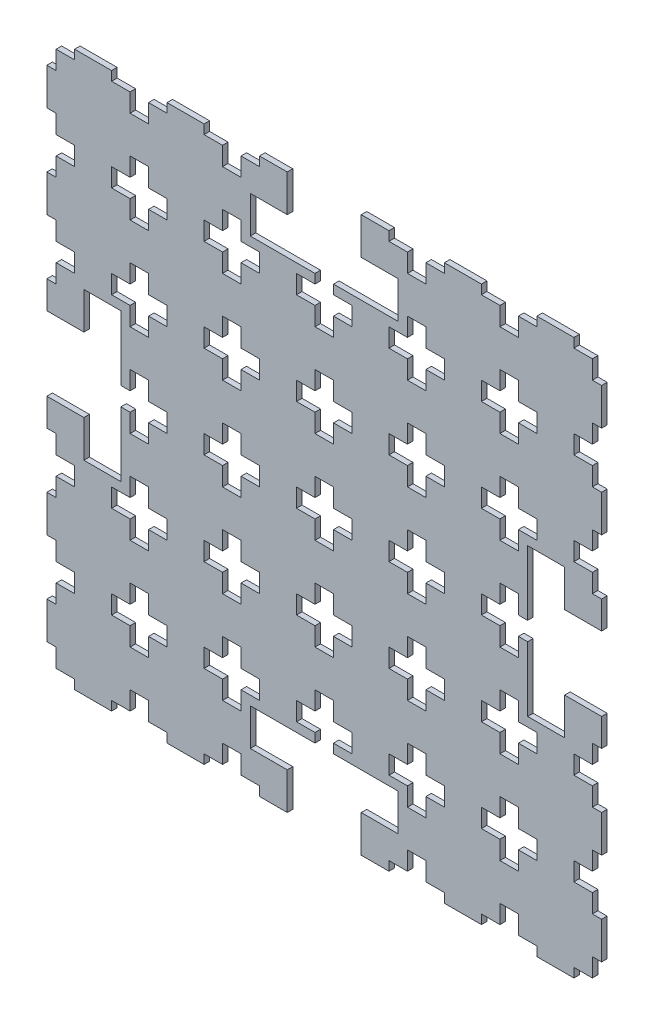
SolidWorks part; units mm, degrees
ref_plane "Plan de face" through (0, 0, 0) normal (0, 0, 1) x (1, 0, 0)
ref_plane "Plan de dessus" through (0, 0, 0) normal (0, 1, 0) x (1, 0, 0)
ref_plane "Plan de droite" through (0, 0, 0) normal (1, 0, 0) x (0, 0, -1)
sketch "Esquisse1" plane through (0, 0, 0) normal (0, 0, 1) x (1, 0, 0)
  line L1 (-218.6403, 173.0618) -> (81.3597, 173.0618)
  line L2 (-218.6403, 173.0618) -> (-218.6403, -126.9382)
  line L3 (-218.6403, -126.9382) -> (81.3597, -126.9382)
  line L4 (81.3597, 173.0618) -> (81.3597, -126.9382)
  dimension "D1" = 300
  dimension "D2" = 300
extrude "Boss.-Extru.1" add sketch "Esquisse1" along normal blind 3
sketch "Esquisse2" plane through (0, 0, 0) normal (0, 0, -1) x (-1, 0, 0)
  line L0 (-81.3597, 138.0618) -> (-76.3597, 138.0618)
  line L1 (183.6403, 173.0618) -> (183.6403, 168.0618)
  line L2 (-81.3597, -126.9382) -> (-81.3597, 173.0618) construction
  line L3 (-76.3597, 138.0618) -> (-76.3597, 128.0618)
  line L4 (-76.3597, 128.0618) -> (-66.3597, 128.0618)
  line L5 (-66.3597, 128.0618) -> (-66.3597, 118.0618)
  line L6 (-66.3597, 118.0618) -> (-76.3597, 118.0618)
  line L7 (-76.3597, 118.0618) -> (-76.3597, 108.0618)
  line L8 (13.6403, 128.0618) -> (13.6403, 138.0618)
  line L9 (-76.3597, 108.0618) -> (-81.3597, 108.0618)
  line L10 (-81.3597, 88.0618) -> (-76.3597, 88.0618)
  line L11 (-76.3597, 88.0618) -> (-76.3597, 78.0618)
  line L12 (-76.3597, 78.0618) -> (-66.3597, 78.0618)
  line L13 (-66.3597, 78.0618) -> (-66.3597, 68.0618)
  line L14 (-66.3597, 68.0618) -> (-76.3597, 68.0618)
  line L15 (-76.3597, 68.0618) -> (-76.3597, 58.0618)
  line L16 (-76.3597, 58.0618) -> (-81.3597, 58.0618)
  line L17 (-81.3597, 38.0618) -> (-76.3597, 38.0618)
  line L18 (-76.3597, 38.0618) -> (-76.3597, 28.0618)
  line L19 (-76.3597, 28.0618) -> (-66.3597, 28.0618)
  line L20 (-66.3597, 28.0618) -> (-66.3597, 18.0618)
  line L21 (-66.3597, 18.0618) -> (-76.3597, 18.0618)
  line L22 (-76.3597, 18.0618) -> (-76.3597, 8.0618)
  line L23 (-76.3597, 8.0618) -> (-81.3597, 8.0618)
  line L24 (-81.3597, -11.9382) -> (-76.3597, -11.9382)
  line L25 (-76.3597, -11.9382) -> (-76.3597, -21.9382)
  line L26 (-76.3597, -21.9382) -> (-66.3597, -21.9382)
  line L27 (-66.3597, -21.9382) -> (-66.3597, -31.9382)
  line L28 (-66.3597, -31.9382) -> (-76.3597, -31.9382)
  line L29 (-76.3597, -31.9382) -> (-76.3597, -41.9382)
  line L30 (-76.3597, -41.9382) -> (-81.3597, -41.9382)
  line L31 (-81.3597, -61.9382) -> (-76.3597, -61.9382)
  line L32 (-76.3597, -61.9382) -> (-76.3597, -71.9382)
  line L33 (-76.3597, -71.9382) -> (-66.3597, -71.9382)
  line L34 (-66.3597, -71.9382) -> (-66.3597, -81.9382)
  line L35 (-66.3597, -81.9382) -> (-76.3597, -81.9382)
  line L36 (-76.3597, -81.9382) -> (-76.3597, -91.9382)
  line L37 (-76.3597, -91.9382) -> (-81.3597, -91.9382)
  line L38 (-81.3597, -111.9382) -> (-76.3597, -111.9382)
  line L39 (-76.3597, -111.9382) -> (-76.3597, -121.9382)
  line L40 (-76.3597, -121.9382) -> (-66.3597, -121.9382)
  line L41 (-66.3597, -121.9382) -> (-66.3597, -126.9382)
  line L42 (218.6403, -126.9382) -> (-81.3597, -126.9382) construction
  line L43 (-81.3597, 173.0618) -> (218.6403, 173.0618) construction
  line L44 (-81.3597, 173.0618) -> (218.6403, 173.0618) construction
  line L45 (-66.3597, -131.9382) -> (-76.3597, -131.9382) [skipped]
  line L46 (-76.3597, -131.9382) -> (-76.3597, -141.9382) [skipped]
  line L47 (-76.3597, -141.9382) -> (-81.3597, -141.9382) [skipped]
  line L48 (-66.3597, -121.9382) -> (-66.3597, -131.9382) [skipped]
  line L49 (183.6403, 168.0618) -> (173.6403, 168.0618)
  line L50 (173.6403, 168.0618) -> (173.6403, 158.0618)
  line L51 (173.6403, 158.0618) -> (163.6403, 158.0618)
  line L52 (163.6403, 158.0618) -> (163.6403, 168.0618)
  line L53 (163.6403, 168.0618) -> (153.6403, 168.0618)
  line L54 (153.6403, 168.0618) -> (153.6403, 173.0618)
  line L55 (153.6403, 173.0618) -> (183.6403, 173.0618)
  line L56 (133.6403, 173.0618) -> (133.6403, 168.0618)
  line L57 (133.6403, 168.0618) -> (123.6403, 168.0618)
  line L58 (123.6403, 168.0618) -> (123.6403, 158.0618)
  line L59 (123.6403, 158.0618) -> (113.6403, 158.0618)
  line L60 (113.6403, 158.0618) -> (113.6403, 168.0618)
  line L61 (-36.3597, 128.0618) -> (-36.3597, 138.0618)
  line L62 (-36.3597, 138.0618) -> (-26.3597, 138.0618)
  line L63 (-26.3597, 138.0618) -> (-26.3597, 128.0618)
  line L64 (-26.3597, 128.0618) -> (-16.3597, 128.0618)
  line L65 (-16.3597, 128.0618) -> (-16.3597, 118.0618)
  line L66 (13.6403, 138.0618) -> (23.6403, 138.0618)
  line L67 (3.6403, 128.0618) -> (13.6403, 128.0618)
  line L68 (3.6403, 118.0618) -> (3.6403, 128.0618)
  line L69 (13.6403, 118.0618) -> (3.6403, 118.0618)
  line L70 (13.6403, 108.0618) -> (13.6403, 118.0618)
  line L71 (23.6403, 108.0618) -> (13.6403, 108.0618)
  line L72 (23.6403, 118.0618) -> (23.6403, 108.0618)
  line L73 (33.6403, 118.0618) -> (23.6403, 118.0618)
  line L74 (33.6403, 128.0618) -> (33.6403, 118.0618)
  line L75 (23.6403, 128.0618) -> (33.6403, 128.0618)
  line L76 (23.6403, 138.0618) -> (23.6403, 128.0618)
  line L77 (63.6403, 128.0618) -> (63.6403, 138.0618)
  line L78 (63.6403, 138.0618) -> (73.6403, 138.0618)
  line L79 (53.6403, 128.0618) -> (63.6403, 128.0618)
  line L80 (53.6403, 118.0618) -> (53.6403, 128.0618)
  line L81 (63.6403, 118.0618) -> (53.6403, 118.0618)
  line L82 (63.6403, 108.0618) -> (63.6403, 118.0618)
  line L83 (73.6403, 108.0618) -> (63.6403, 108.0618)
  line L84 (73.6403, 118.0618) -> (73.6403, 108.0618)
  line L85 (83.6403, 118.0618) -> (73.6403, 118.0618)
  line L86 (83.6403, 128.0618) -> (83.6403, 118.0618)
  line L87 (73.6403, 128.0618) -> (83.6403, 128.0618)
  line L88 (73.6403, 138.0618) -> (73.6403, 128.0618)
  line L89 (113.6403, 128.0618) -> (113.6403, 138.0618)
  line L90 (113.6403, 138.0618) -> (123.6403, 138.0618)
  line L91 (103.6403, 128.0618) -> (113.6403, 128.0618)
  line L92 (103.6403, 118.0618) -> (103.6403, 128.0618)
  line L93 (113.6403, 118.0618) -> (103.6403, 118.0618)
  line L94 (113.6403, 108.0618) -> (113.6403, 118.0618)
  line L95 (123.6403, 108.0618) -> (113.6403, 108.0618)
  line L96 (123.6403, 118.0618) -> (123.6403, 108.0618)
  line L97 (133.6403, 118.0618) -> (123.6403, 118.0618)
  line L98 (133.6403, 128.0618) -> (133.6403, 118.0618)
  line L99 (123.6403, 128.0618) -> (133.6403, 128.0618)
  line L100 (123.6403, 138.0618) -> (123.6403, 128.0618)
  line L101 (163.6403, 128.0618) -> (163.6403, 138.0618)
  line L102 (163.6403, 138.0618) -> (173.6403, 138.0618)
  line L103 (153.6403, 128.0618) -> (163.6403, 128.0618)
  line L104 (153.6403, 118.0618) -> (153.6403, 128.0618)
  line L105 (163.6403, 118.0618) -> (153.6403, 118.0618)
  line L106 (163.6403, 108.0618) -> (163.6403, 118.0618)
  line L107 (173.6403, 108.0618) -> (163.6403, 108.0618)
  line L108 (173.6403, 118.0618) -> (173.6403, 108.0618)
  line L109 (183.6403, 118.0618) -> (173.6403, 118.0618)
  line L110 (183.6403, 128.0618) -> (183.6403, 118.0618)
  line L111 (173.6403, 128.0618) -> (183.6403, 128.0618)
  line L112 (173.6403, 138.0618) -> (173.6403, 128.0618)
  line L113 (213.6403, 128.0618) -> (213.6403, 138.0618)
  line L114 (213.6403, 138.0618) -> (223.6403, 138.0618)
  line L115 (203.6403, 128.0618) -> (213.6403, 128.0618)
  line L116 (203.6403, 118.0618) -> (203.6403, 128.0618)
  line L117 (213.6403, 118.0618) -> (203.6403, 118.0618)
  line L118 (213.6403, 108.0618) -> (213.6403, 118.0618)
  line L119 (223.6403, 108.0618) -> (213.6403, 108.0618)
  line L120 (223.6403, 118.0618) -> (223.6403, 108.0618)
  line L121 (233.6403, 118.0618) -> (223.6403, 118.0618)
  line L122 (233.6403, 128.0618) -> (233.6403, 118.0618)
  line L123 (223.6403, 128.0618) -> (233.6403, 128.0618)
  line L124 (223.6403, 138.0618) -> (223.6403, 128.0618)
  line L125 (113.6403, 168.0618) -> (103.6403, 168.0618)
  line L126 (103.6403, 168.0618) -> (103.6403, 173.0618)
  line L127 (103.6403, 173.0618) -> (133.6403, 173.0618)
  line L128 (83.6403, 173.0618) -> (83.6403, 168.0618)
  line L129 (83.6403, 168.0618) -> (73.6403, 168.0618)
  line L130 (73.6403, 168.0618) -> (73.6403, 158.0618)
  line L131 (73.6403, 158.0618) -> (63.6403, 158.0618)
  line L132 (63.6403, 158.0618) -> (63.6403, 168.0618)
  line L133 (63.6403, 168.0618) -> (53.6403, 168.0618)
  line L134 (53.6403, 168.0618) -> (53.6403, 173.0618)
  line L135 (83.6403, 173.0618) -> (53.6403, 173.0618)
  line L136 (33.6403, 173.0618) -> (33.6403, 168.0618)
  line L137 (33.6403, 168.0618) -> (23.6403, 168.0618)
  line L138 (23.6403, 168.0618) -> (23.6403, 158.0618)
  line L139 (23.6403, 158.0618) -> (13.6403, 158.0618)
  line L140 (13.6403, 158.0618) -> (13.6403, 168.0618)
  line L141 (13.6403, 168.0618) -> (3.6403, 168.0618)
  line L142 (3.6403, 168.0618) -> (3.6403, 173.0618)
  line L143 (33.6403, 173.0618) -> (3.6403, 173.0618)
  line L144 (-16.3597, 173.0618) -> (-16.3597, 168.0618)
  line L145 (-16.3597, 168.0618) -> (-26.3597, 168.0618)
  line L146 (-26.3597, 168.0618) -> (-26.3597, 158.0618)
  line L147 (-26.3597, 158.0618) -> (-36.3597, 158.0618)
  line L148 (-36.3597, 158.0618) -> (-36.3597, 168.0618)
  line L149 (-36.3597, 168.0618) -> (-46.3597, 168.0618)
  line L150 (-46.3597, 168.0618) -> (-46.3597, 173.0618)
  line L151 (-46.3597, 173.0618) -> (-16.3597, 173.0618)
  line L180 (218.6403, 173.0618) -> (218.6403, -126.9382) construction
  line L186 (13.6403, 78.0618) -> (13.6403, 88.0618)
  line L187 (13.6403, 88.0618) -> (23.6403, 88.0618)
  line L188 (3.6403, 78.0618) -> (13.6403, 78.0618)
  line L189 (3.6403, 68.0618) -> (3.6403, 78.0618)
  line L190 (13.6403, 68.0618) -> (3.6403, 68.0618)
  line L191 (13.6403, 58.0618) -> (13.6403, 68.0618)
  line L192 (23.6403, 58.0618) -> (13.6403, 58.0618)
  line L193 (23.6403, 68.0618) -> (23.6403, 58.0618)
  line L194 (33.6403, 68.0618) -> (23.6403, 68.0618)
  line L195 (33.6403, 78.0618) -> (33.6403, 68.0618)
  line L196 (23.6403, 78.0618) -> (33.6403, 78.0618)
  line L197 (23.6403, 88.0618) -> (23.6403, 78.0618)
  line L198 (63.6403, 78.0618) -> (63.6403, 88.0618)
  line L199 (63.6403, 88.0618) -> (73.6403, 88.0618)
  line L200 (53.6403, 78.0618) -> (63.6403, 78.0618)
  line L201 (53.6403, 68.0618) -> (53.6403, 78.0618)
  line L202 (63.6403, 68.0618) -> (53.6403, 68.0618)
  line L203 (63.6403, 58.0618) -> (63.6403, 68.0618)
  line L204 (73.6403, 58.0618) -> (63.6403, 58.0618)
  line L205 (73.6403, 68.0618) -> (73.6403, 58.0618)
  line L206 (83.6403, 68.0618) -> (73.6403, 68.0618)
  line L207 (83.6403, 78.0618) -> (83.6403, 68.0618)
  line L208 (73.6403, 78.0618) -> (83.6403, 78.0618)
  line L209 (73.6403, 88.0618) -> (73.6403, 78.0618)
  line L210 (113.6403, 78.0618) -> (113.6403, 88.0618)
  line L211 (113.6403, 88.0618) -> (123.6403, 88.0618)
  line L212 (103.6403, 78.0618) -> (113.6403, 78.0618)
  line L213 (103.6403, 68.0618) -> (103.6403, 78.0618)
  line L214 (113.6403, 68.0618) -> (103.6403, 68.0618)
  line L215 (113.6403, 58.0618) -> (113.6403, 68.0618)
  line L216 (123.6403, 58.0618) -> (113.6403, 58.0618)
  line L217 (123.6403, 68.0618) -> (123.6403, 58.0618)
  line L218 (133.6403, 68.0618) -> (123.6403, 68.0618)
  line L219 (133.6403, 78.0618) -> (133.6403, 68.0618)
  line L220 (123.6403, 78.0618) -> (133.6403, 78.0618)
  line L221 (123.6403, 88.0618) -> (123.6403, 78.0618)
  line L222 (163.6403, 78.0618) -> (163.6403, 88.0618)
  line L223 (163.6403, 88.0618) -> (173.6403, 88.0618)
  line L224 (153.6403, 78.0618) -> (163.6403, 78.0618)
  line L225 (153.6403, 68.0618) -> (153.6403, 78.0618)
  line L226 (163.6403, 68.0618) -> (153.6403, 68.0618)
  line L227 (163.6403, 58.0618) -> (163.6403, 68.0618)
  line L228 (173.6403, 58.0618) -> (163.6403, 58.0618)
  line L229 (173.6403, 68.0618) -> (173.6403, 58.0618)
  line L230 (183.6403, 68.0618) -> (173.6403, 68.0618)
  line L231 (183.6403, 78.0618) -> (183.6403, 68.0618)
  line L232 (173.6403, 78.0618) -> (183.6403, 78.0618)
  line L233 (173.6403, 88.0618) -> (173.6403, 78.0618)
  line L234 (213.6403, 78.0618) -> (213.6403, 88.0618)
  line L235 (213.6403, 88.0618) -> (223.6403, 88.0618)
  line L236 (203.6403, 78.0618) -> (213.6403, 78.0618)
  line L237 (203.6403, 68.0618) -> (203.6403, 78.0618)
  line L238 (213.6403, 68.0618) -> (203.6403, 68.0618)
  line L239 (213.6403, 58.0618) -> (213.6403, 68.0618)
  line L240 (223.6403, 58.0618) -> (213.6403, 58.0618)
  line L241 (223.6403, 68.0618) -> (223.6403, 58.0618)
  line L242 (233.6403, 68.0618) -> (223.6403, 68.0618)
  line L243 (233.6403, 78.0618) -> (233.6403, 68.0618)
  line L244 (223.6403, 78.0618) -> (233.6403, 78.0618)
  line L245 (223.6403, 88.0618) -> (223.6403, 78.0618)
  line L246 (13.6403, 28.0618) -> (13.6403, 38.0618)
  line L247 (13.6403, 38.0618) -> (23.6403, 38.0618)
  line L248 (3.6403, 28.0618) -> (13.6403, 28.0618)
  line L249 (3.6403, 18.0618) -> (3.6403, 28.0618)
  line L250 (13.6403, 18.0618) -> (3.6403, 18.0618)
  line L251 (13.6403, 8.0618) -> (13.6403, 18.0618)
  line L252 (23.6403, 8.0618) -> (13.6403, 8.0618)
  line L253 (23.6403, 18.0618) -> (23.6403, 8.0618)
  line L254 (33.6403, 18.0618) -> (23.6403, 18.0618)
  line L255 (33.6403, 28.0618) -> (33.6403, 18.0618)
  line L256 (23.6403, 28.0618) -> (33.6403, 28.0618)
  line L257 (23.6403, 38.0618) -> (23.6403, 28.0618)
  line L258 (63.6403, 28.0618) -> (63.6403, 38.0618)
  line L259 (63.6403, 38.0618) -> (73.6403, 38.0618)
  line L260 (53.6403, 28.0618) -> (63.6403, 28.0618)
  line L261 (53.6403, 18.0618) -> (53.6403, 28.0618)
  line L262 (63.6403, 18.0618) -> (53.6403, 18.0618)
  line L263 (63.6403, 8.0618) -> (63.6403, 18.0618)
  line L264 (73.6403, 8.0618) -> (63.6403, 8.0618)
  line L265 (73.6403, 18.0618) -> (73.6403, 8.0618)
  line L266 (83.6403, 18.0618) -> (73.6403, 18.0618)
  line L267 (83.6403, 28.0618) -> (83.6403, 18.0618)
  line L268 (73.6403, 28.0618) -> (83.6403, 28.0618)
  line L269 (73.6403, 38.0618) -> (73.6403, 28.0618)
  line L270 (113.6403, 28.0618) -> (113.6403, 38.0618)
  line L271 (113.6403, 38.0618) -> (123.6403, 38.0618)
  line L272 (103.6403, 28.0618) -> (113.6403, 28.0618)
  line L273 (103.6403, 18.0618) -> (103.6403, 28.0618)
  line L274 (113.6403, 18.0618) -> (103.6403, 18.0618)
  line L275 (113.6403, 8.0618) -> (113.6403, 18.0618)
  line L276 (123.6403, 8.0618) -> (113.6403, 8.0618)
  line L277 (123.6403, 18.0618) -> (123.6403, 8.0618)
  line L278 (133.6403, 18.0618) -> (123.6403, 18.0618)
  line L279 (133.6403, 28.0618) -> (133.6403, 18.0618)
  line L280 (123.6403, 28.0618) -> (133.6403, 28.0618)
  line L281 (123.6403, 38.0618) -> (123.6403, 28.0618)
  line L282 (163.6403, 28.0618) -> (163.6403, 38.0618)
  line L283 (163.6403, 38.0618) -> (173.6403, 38.0618)
  line L284 (153.6403, 28.0618) -> (163.6403, 28.0618)
  line L285 (153.6403, 18.0618) -> (153.6403, 28.0618)
  line L286 (163.6403, 18.0618) -> (153.6403, 18.0618)
  line L287 (163.6403, 8.0618) -> (163.6403, 18.0618)
  line L288 (173.6403, 8.0618) -> (163.6403, 8.0618)
  line L289 (173.6403, 18.0618) -> (173.6403, 8.0618)
  line L290 (183.6403, 18.0618) -> (173.6403, 18.0618)
  line L291 (183.6403, 28.0618) -> (183.6403, 18.0618)
  line L292 (173.6403, 28.0618) -> (183.6403, 28.0618)
  line L293 (173.6403, 38.0618) -> (173.6403, 28.0618)
  line L294 (213.6403, 28.0618) -> (213.6403, 38.0618)
  line L295 (213.6403, 38.0618) -> (223.6403, 38.0618)
  line L296 (203.6403, 28.0618) -> (213.6403, 28.0618)
  line L297 (203.6403, 18.0618) -> (203.6403, 28.0618)
  line L298 (-66.3597, 173.0618) -> (-66.3597, 168.0618)
  line L299 (-66.3597, 168.0618) -> (-76.3597, 168.0618)
  line L300 (-76.3597, 168.0618) -> (-76.3597, 158.0618)
  line L301 (-76.3597, 158.0618) -> (-81.3597, 158.0618)
  line L302 (218.6403, 158.0618) -> (213.6403, 158.0618)
  line L303 (213.6403, 18.0618) -> (203.6403, 18.0618)
  line L304 (213.6403, 8.0618) -> (213.6403, 18.0618)
  line L305 (223.6403, 8.0618) -> (213.6403, 8.0618)
  line L306 (223.6403, 18.0618) -> (223.6403, 8.0618)
  line L307 (233.6403, 18.0618) -> (223.6403, 18.0618)
  line L308 (233.6403, 28.0618) -> (233.6403, 18.0618)
  line L309 (223.6403, 28.0618) -> (233.6403, 28.0618)
  line L310 (223.6403, 38.0618) -> (223.6403, 28.0618)
  line L311 (13.6403, -21.9382) -> (13.6403, -11.9382)
  line L312 (13.6403, -11.9382) -> (23.6403, -11.9382)
  line L313 (3.6403, -21.9382) -> (13.6403, -21.9382)
  line L314 (3.6403, -31.9382) -> (3.6403, -21.9382)
  line L315 (13.6403, -31.9382) -> (3.6403, -31.9382)
  line L316 (13.6403, -41.9382) -> (13.6403, -31.9382)
  line L317 (23.6403, -41.9382) -> (13.6403, -41.9382)
  line L318 (23.6403, -31.9382) -> (23.6403, -41.9382)
  line L319 (33.6403, -31.9382) -> (23.6403, -31.9382)
  line L320 (33.6403, -21.9382) -> (33.6403, -31.9382)
  line L321 (23.6403, -21.9382) -> (33.6403, -21.9382)
  line L322 (23.6403, -11.9382) -> (23.6403, -21.9382)
  line L323 (63.6403, -21.9382) -> (63.6403, -11.9382)
  line L324 (63.6403, -11.9382) -> (73.6403, -11.9382)
  line L325 (53.6403, -21.9382) -> (63.6403, -21.9382)
  line L326 (53.6403, -31.9382) -> (53.6403, -21.9382)
  line L327 (63.6403, -31.9382) -> (53.6403, -31.9382)
  line L328 (63.6403, -41.9382) -> (63.6403, -31.9382)
  line L329 (73.6403, -41.9382) -> (63.6403, -41.9382)
  line L330 (73.6403, -31.9382) -> (73.6403, -41.9382)
  line L331 (83.6403, -31.9382) -> (73.6403, -31.9382)
  line L332 (83.6403, -21.9382) -> (83.6403, -31.9382)
  line L333 (73.6403, -21.9382) -> (83.6403, -21.9382)
  line L334 (73.6403, -11.9382) -> (73.6403, -21.9382)
  line L335 (113.6403, -21.9382) -> (113.6403, -11.9382)
  line L336 (113.6403, -11.9382) -> (123.6403, -11.9382)
  line L337 (103.6403, -21.9382) -> (113.6403, -21.9382)
  line L338 (103.6403, -31.9382) -> (103.6403, -21.9382)
  line L339 (113.6403, -31.9382) -> (103.6403, -31.9382)
  line L340 (113.6403, -41.9382) -> (113.6403, -31.9382)
  line L341 (123.6403, -41.9382) -> (113.6403, -41.9382)
  line L342 (123.6403, -31.9382) -> (123.6403, -41.9382)
  line L343 (133.6403, -31.9382) -> (123.6403, -31.9382)
  line L344 (133.6403, -21.9382) -> (133.6403, -31.9382)
  line L345 (123.6403, -21.9382) -> (133.6403, -21.9382)
  line L346 (123.6403, -11.9382) -> (123.6403, -21.9382)
  line L347 (163.6403, -21.9382) -> (163.6403, -11.9382)
  line L348 (163.6403, -11.9382) -> (173.6403, -11.9382)
  line L349 (153.6403, -21.9382) -> (163.6403, -21.9382)
  line L350 (153.6403, -31.9382) -> (153.6403, -21.9382)
  line L351 (163.6403, -31.9382) -> (153.6403, -31.9382)
  line L352 (163.6403, -41.9382) -> (163.6403, -31.9382)
  line L353 (173.6403, -41.9382) -> (163.6403, -41.9382)
  line L354 (173.6403, -31.9382) -> (173.6403, -41.9382)
  line L355 (183.6403, -31.9382) -> (173.6403, -31.9382)
  line L356 (213.6403, 158.0618) -> (213.6403, 168.0618)
  line L357 (213.6403, 168.0618) -> (203.6403, 168.0618)
  line L358 (203.6403, 168.0618) -> (203.6403, 173.0618)
  line L363 (183.6403, -21.9382) -> (183.6403, -31.9382)
  line L364 (173.6403, -21.9382) -> (183.6403, -21.9382)
  line L365 (-16.3597, 118.0618) -> (-26.3597, 118.0618)
  line L366 (173.6403, -11.9382) -> (173.6403, -21.9382)
  line L367 (213.6403, -21.9382) -> (213.6403, -11.9382)
  line L368 (213.6403, -11.9382) -> (223.6403, -11.9382)
  line L369 (203.6403, -21.9382) -> (213.6403, -21.9382)
  line L370 (203.6403, -31.9382) -> (203.6403, -21.9382)
  line L371 (-26.3597, 118.0618) -> (-26.3597, 108.0618)
  line L372 (-26.3597, 108.0618) -> (-36.3597, 108.0618)
  line L373 (-36.3597, 108.0618) -> (-36.3597, 118.0618)
  line L374 (-36.3597, 118.0618) -> (-46.3597, 118.0618)
  line L375 (-46.3597, 118.0618) -> (-46.3597, 128.0618)
  line L376 (-46.3597, 128.0618) -> (-36.3597, 128.0618)
  line L377 (213.6403, -31.9382) -> (203.6403, -31.9382)
  line L378 (213.6403, -41.9382) -> (213.6403, -31.9382)
  line L379 (223.6403, -41.9382) -> (213.6403, -41.9382)
  line L380 (223.6403, -31.9382) -> (223.6403, -41.9382)
  line L381 (233.6403, -31.9382) -> (223.6403, -31.9382)
  line L382 (233.6403, -21.9382) -> (233.6403, -31.9382)
  line L383 (223.6403, -21.9382) -> (233.6403, -21.9382)
  line L384 (223.6403, -11.9382) -> (223.6403, -21.9382)
  line L385 (13.6403, -71.9382) -> (13.6403, -61.9382)
  line L386 (13.6403, -61.9382) -> (23.6403, -61.9382)
  line L387 (3.6403, -71.9382) -> (13.6403, -71.9382)
  line L388 (3.6403, -81.9382) -> (3.6403, -71.9382)
  line L389 (13.6403, -81.9382) -> (3.6403, -81.9382)
  line L390 (13.6403, -91.9382) -> (13.6403, -81.9382)
  line L391 (23.6403, -91.9382) -> (13.6403, -91.9382)
  line L392 (23.6403, -81.9382) -> (23.6403, -91.9382)
  line L393 (33.6403, -81.9382) -> (23.6403, -81.9382)
  line L394 (33.6403, -71.9382) -> (33.6403, -81.9382)
  line L395 (23.6403, -71.9382) -> (33.6403, -71.9382)
  line L396 (23.6403, -61.9382) -> (23.6403, -71.9382)
  line L397 (63.6403, -71.9382) -> (63.6403, -61.9382)
  line L398 (63.6403, -61.9382) -> (73.6403, -61.9382)
  line L399 (53.6403, -71.9382) -> (63.6403, -71.9382)
  line L400 (53.6403, -81.9382) -> (53.6403, -71.9382)
  line L401 (63.6403, -81.9382) -> (53.6403, -81.9382)
  line L402 (63.6403, -91.9382) -> (63.6403, -81.9382)
  line L403 (73.6403, -91.9382) -> (63.6403, -91.9382)
  line L404 (73.6403, -81.9382) -> (73.6403, -91.9382)
  line L405 (83.6403, -81.9382) -> (73.6403, -81.9382)
  line L406 (83.6403, -71.9382) -> (83.6403, -81.9382)
  line L407 (73.6403, -71.9382) -> (83.6403, -71.9382)
  line L408 (73.6403, -61.9382) -> (73.6403, -71.9382)
  line L409 (113.6403, -71.9382) -> (113.6403, -61.9382)
  line L410 (113.6403, -61.9382) -> (123.6403, -61.9382)
  line L411 (103.6403, -71.9382) -> (113.6403, -71.9382)
  line L412 (103.6403, -81.9382) -> (103.6403, -71.9382)
  line L413 (113.6403, -81.9382) -> (103.6403, -81.9382)
  line L414 (113.6403, -91.9382) -> (113.6403, -81.9382)
  line L415 (123.6403, -91.9382) -> (113.6403, -91.9382)
  line L416 (123.6403, -81.9382) -> (123.6403, -91.9382)
  line L417 (133.6403, -81.9382) -> (123.6403, -81.9382)
  line L418 (133.6403, -71.9382) -> (133.6403, -81.9382)
  line L419 (123.6403, -71.9382) -> (133.6403, -71.9382)
  line L420 (123.6403, -61.9382) -> (123.6403, -71.9382)
  line L421 (163.6403, -71.9382) -> (163.6403, -61.9382)
  line L422 (163.6403, -61.9382) -> (173.6403, -61.9382)
  line L423 (153.6403, -71.9382) -> (163.6403, -71.9382)
  line L424 (153.6403, -81.9382) -> (153.6403, -71.9382)
  line L425 (163.6403, -81.9382) -> (153.6403, -81.9382)
  line L426 (163.6403, -91.9382) -> (163.6403, -81.9382)
  line L427 (173.6403, -91.9382) -> (163.6403, -91.9382)
  line L428 (173.6403, -81.9382) -> (173.6403, -91.9382)
  line L429 (183.6403, -81.9382) -> (173.6403, -81.9382)
  line L430 (183.6403, -71.9382) -> (183.6403, -81.9382)
  line L431 (173.6403, -71.9382) -> (183.6403, -71.9382)
  line L432 (173.6403, -61.9382) -> (173.6403, -71.9382)
  line L433 (213.6403, -71.9382) -> (213.6403, -61.9382)
  line L434 (213.6403, -61.9382) -> (223.6403, -61.9382)
  line L435 (203.6403, -71.9382) -> (213.6403, -71.9382)
  line L436 (203.6403, -81.9382) -> (203.6403, -71.9382)
  line L437 (213.6403, -81.9382) -> (203.6403, -81.9382)
  line L438 (213.6403, -91.9382) -> (213.6403, -81.9382)
  line L439 (223.6403, -91.9382) -> (213.6403, -91.9382)
  line L440 (223.6403, -81.9382) -> (223.6403, -91.9382)
  line L441 (233.6403, -81.9382) -> (223.6403, -81.9382)
  line L442 (233.6403, -71.9382) -> (233.6403, -81.9382)
  line L443 (223.6403, -71.9382) -> (233.6403, -71.9382)
  line L444 (223.6403, -61.9382) -> (223.6403, -71.9382)
  line L445 (13.6403, -121.9382) -> (13.6403, -111.9382)
  line L446 (13.6403, -111.9382) -> (23.6403, -111.9382)
  line L447 (3.6403, -121.9382) -> (13.6403, -121.9382)
  line L448 (3.6403, -131.9382) -> (3.6403, -121.9382)
  line L449 (13.6403, -131.9382) -> (3.6403, -131.9382)
  line L450 (13.6403, -141.9382) -> (13.6403, -131.9382)
  line L451 (23.6403, -141.9382) -> (13.6403, -141.9382)
  line L452 (23.6403, -131.9382) -> (23.6403, -141.9382)
  line L453 (33.6403, -131.9382) -> (23.6403, -131.9382)
  line L454 (33.6403, -121.9382) -> (33.6403, -131.9382)
  line L455 (23.6403, -121.9382) -> (33.6403, -121.9382)
  line L456 (23.6403, -111.9382) -> (23.6403, -121.9382)
  line L457 (63.6403, -121.9382) -> (63.6403, -111.9382)
  line L458 (63.6403, -111.9382) -> (73.6403, -111.9382)
  line L459 (53.6403, -121.9382) -> (63.6403, -121.9382)
  line L460 (53.6403, -131.9382) -> (53.6403, -121.9382)
  line L461 (63.6403, -131.9382) -> (53.6403, -131.9382)
  line L462 (63.6403, -141.9382) -> (63.6403, -131.9382)
  line L463 (73.6403, -141.9382) -> (63.6403, -141.9382)
  line L464 (73.6403, -131.9382) -> (73.6403, -141.9382)
  line L465 (83.6403, -131.9382) -> (73.6403, -131.9382)
  line L466 (83.6403, -121.9382) -> (83.6403, -131.9382)
  line L467 (73.6403, -121.9382) -> (83.6403, -121.9382)
  line L468 (73.6403, -111.9382) -> (73.6403, -121.9382)
  line L469 (113.6403, -121.9382) -> (113.6403, -111.9382)
  line L470 (113.6403, -111.9382) -> (123.6403, -111.9382)
  line L471 (103.6403, -121.9382) -> (113.6403, -121.9382)
  line L472 (103.6403, -131.9382) -> (103.6403, -121.9382)
  line L473 (113.6403, -131.9382) -> (103.6403, -131.9382)
  line L474 (113.6403, -141.9382) -> (113.6403, -131.9382)
  line L475 (123.6403, -141.9382) -> (113.6403, -141.9382)
  line L476 (123.6403, -131.9382) -> (123.6403, -141.9382)
  line L477 (133.6403, -131.9382) -> (123.6403, -131.9382)
  line L478 (133.6403, -121.9382) -> (133.6403, -131.9382)
  line L479 (123.6403, -121.9382) -> (133.6403, -121.9382)
  line L480 (123.6403, -111.9382) -> (123.6403, -121.9382)
  line L481 (163.6403, -121.9382) -> (163.6403, -111.9382)
  line L482 (163.6403, -111.9382) -> (173.6403, -111.9382)
  line L483 (153.6403, -121.9382) -> (163.6403, -121.9382)
  line L484 (153.6403, -131.9382) -> (153.6403, -121.9382)
  line L485 (163.6403, -131.9382) -> (153.6403, -131.9382)
  line L486 (163.6403, -141.9382) -> (163.6403, -131.9382)
  line L487 (203.6403, 173.0618) -> (218.6403, 173.0618)
  line L488 (218.6403, 173.0618) -> (218.6403, 158.0618)
  line L489 (-81.3597, 158.0618) -> (-81.3597, 173.0618)
  line L490 (-81.3597, 173.0618) -> (-66.3597, 173.0618)
  line L491 (-81.3597, 138.0618) -> (-81.3597, 108.0618)
  line L492 (-81.3597, 88.0618) -> (-81.3597, 58.0618)
  line L494 (-81.3597, 38.0618) -> (-81.3597, 8.0618)
  line L495 (-81.3597, -11.9382) -> (-81.3597, -41.9382)
  line L496 (-81.3597, -61.9382) -> (-81.3597, -91.9382)
  line L497 (-81.3597, -111.9382) -> (-81.3597, -126.9382)
  line L498 (-81.3597, -126.9382) -> (-66.3597, -126.9382)
  line L567 (173.6403, -141.9382) -> (163.6403, -141.9382)
  line L568 (173.6403, -131.9382) -> (173.6403, -141.9382)
  line L569 (183.6403, -131.9382) -> (173.6403, -131.9382)
  line L570 (183.6403, -121.9382) -> (183.6403, -131.9382)
  line L571 (173.6403, -121.9382) -> (183.6403, -121.9382)
  line L572 (173.6403, -111.9382) -> (173.6403, -121.9382)
  line L573 (213.6403, -121.9382) -> (213.6403, -111.9382)
  line L574 (213.6403, -111.9382) -> (223.6403, -111.9382)
  line L575 (203.6403, -121.9382) -> (213.6403, -121.9382)
  line L576 (203.6403, -131.9382) -> (203.6403, -121.9382)
  line L577 (213.6403, -131.9382) -> (203.6403, -131.9382)
  line L578 (213.6403, -141.9382) -> (213.6403, -131.9382)
  line L579 (223.6403, -141.9382) -> (213.6403, -141.9382)
  line L580 (223.6403, -131.9382) -> (223.6403, -141.9382)
  line L581 (233.6403, -131.9382) -> (223.6403, -131.9382)
  line L582 (233.6403, -121.9382) -> (233.6403, -131.9382)
  line L583 (223.6403, -121.9382) -> (233.6403, -121.9382)
  line L584 (223.6403, -111.9382) -> (223.6403, -121.9382)
  line L585 (13.6403, -171.9382) -> (13.6403, -161.9382)
  line L586 (13.6403, -161.9382) -> (23.6403, -161.9382)
  line L587 (3.6403, -171.9382) -> (13.6403, -171.9382)
  line L588 (3.6403, -181.9382) -> (3.6403, -171.9382)
  line L589 (13.6403, -181.9382) -> (3.6403, -181.9382)
  line L590 (13.6403, -191.9382) -> (13.6403, -181.9382)
  line L591 (23.6403, -191.9382) -> (13.6403, -191.9382)
  line L592 (23.6403, -181.9382) -> (23.6403, -191.9382)
  line L593 (33.6403, -181.9382) -> (23.6403, -181.9382)
  line L594 (33.6403, -171.9382) -> (33.6403, -181.9382)
  line L595 (23.6403, -171.9382) -> (33.6403, -171.9382)
  line L596 (23.6403, -161.9382) -> (23.6403, -171.9382)
  line L597 (63.6403, -171.9382) -> (63.6403, -161.9382)
  line L598 (63.6403, -161.9382) -> (73.6403, -161.9382)
  line L599 (53.6403, -171.9382) -> (63.6403, -171.9382)
  line L600 (53.6403, -181.9382) -> (53.6403, -171.9382)
  line L601 (63.6403, -181.9382) -> (53.6403, -181.9382)
  line L602 (63.6403, -191.9382) -> (63.6403, -181.9382)
  line L603 (73.6403, -191.9382) -> (63.6403, -191.9382)
  line L604 (73.6403, -181.9382) -> (73.6403, -191.9382)
  line L605 (83.6403, -181.9382) -> (73.6403, -181.9382)
  line L606 (83.6403, -171.9382) -> (83.6403, -181.9382)
  line L607 (73.6403, -171.9382) -> (83.6403, -171.9382)
  line L608 (73.6403, -161.9382) -> (73.6403, -171.9382)
  line L609 (113.6403, -171.9382) -> (113.6403, -161.9382)
  line L610 (113.6403, -161.9382) -> (123.6403, -161.9382)
  line L611 (103.6403, -171.9382) -> (113.6403, -171.9382)
  line L612 (103.6403, -181.9382) -> (103.6403, -171.9382)
  line L613 (113.6403, -181.9382) -> (103.6403, -181.9382)
  line L614 (113.6403, -191.9382) -> (113.6403, -181.9382)
  line L615 (123.6403, -191.9382) -> (113.6403, -191.9382)
  line L616 (123.6403, -181.9382) -> (123.6403, -191.9382)
  line L617 (133.6403, -181.9382) -> (123.6403, -181.9382)
  line L618 (133.6403, -171.9382) -> (133.6403, -181.9382)
  line L619 (123.6403, -171.9382) -> (133.6403, -171.9382)
  line L620 (123.6403, -161.9382) -> (123.6403, -171.9382)
  line L657 (63.6403, -221.9382) -> (63.6403, -211.9382)
  line L658 (63.6403, -211.9382) -> (73.6403, -211.9382)
  line L659 (53.6403, -221.9382) -> (63.6403, -221.9382)
  line L660 (53.6403, -231.9382) -> (53.6403, -221.9382)
  line L661 (63.6403, -231.9382) -> (53.6403, -231.9382)
  line L662 (63.6403, -241.9382) -> (63.6403, -231.9382)
  line L663 (73.6403, -241.9382) -> (63.6403, -241.9382)
  line L664 (73.6403, -231.9382) -> (73.6403, -241.9382)
  line L665 (83.6403, -231.9382) -> (73.6403, -231.9382)
  line L666 (83.6403, -221.9382) -> (83.6403, -231.9382)
  line L667 (73.6403, -221.9382) -> (83.6403, -221.9382)
  line L668 (73.6403, -211.9382) -> (73.6403, -221.9382)
  line L765 (-36.3597, 78.0618) -> (-36.3597, 88.0618)
  line L766 (-36.3597, 88.0618) -> (-26.3597, 88.0618)
  line L767 (-46.3597, 78.0618) -> (-36.3597, 78.0618)
  line L768 (-46.3597, 68.0618) -> (-46.3597, 78.0618)
  line L769 (-36.3597, 68.0618) -> (-46.3597, 68.0618)
  line L770 (-36.3597, 58.0618) -> (-36.3597, 68.0618)
  line L771 (-26.3597, 58.0618) -> (-36.3597, 58.0618)
  line L772 (-26.3597, 68.0618) -> (-26.3597, 58.0618)
  line L773 (-16.3597, 68.0618) -> (-26.3597, 68.0618)
  line L774 (-16.3597, 78.0618) -> (-16.3597, 68.0618)
  line L775 (-26.3597, 78.0618) -> (-16.3597, 78.0618)
  line L776 (-26.3597, 88.0618) -> (-26.3597, 78.0618)
  line L777 (-36.3597, 28.0618) -> (-36.3597, 38.0618)
  line L778 (-36.3597, 38.0618) -> (-26.3597, 38.0618)
  line L779 (-46.3597, 28.0618) -> (-36.3597, 28.0618)
  line L780 (-46.3597, 18.0618) -> (-46.3597, 28.0618)
  line L781 (-36.3597, 18.0618) -> (-46.3597, 18.0618)
  line L782 (-36.3597, 8.0618) -> (-36.3597, 18.0618)
  line L783 (-26.3597, 8.0618) -> (-36.3597, 8.0618)
  line L784 (-26.3597, 18.0618) -> (-26.3597, 8.0618)
  line L785 (-16.3597, 18.0618) -> (-26.3597, 18.0618)
  line L786 (-16.3597, 28.0618) -> (-16.3597, 18.0618)
  line L787 (-26.3597, 28.0618) -> (-16.3597, 28.0618)
  line L788 (-26.3597, 38.0618) -> (-26.3597, 28.0618)
  line L789 (-36.3597, -21.9382) -> (-36.3597, -11.9382)
  line L790 (-36.3597, -11.9382) -> (-26.3597, -11.9382)
  line L791 (-46.3597, -21.9382) -> (-36.3597, -21.9382)
  line L792 (-46.3597, -31.9382) -> (-46.3597, -21.9382)
  line L793 (-36.3597, -31.9382) -> (-46.3597, -31.9382)
  line L794 (-36.3597, -41.9382) -> (-36.3597, -31.9382)
  line L795 (-26.3597, -41.9382) -> (-36.3597, -41.9382)
  line L796 (-26.3597, -31.9382) -> (-26.3597, -41.9382)
  line L797 (-16.3597, -31.9382) -> (-26.3597, -31.9382)
  line L798 (-16.3597, -21.9382) -> (-16.3597, -31.9382)
  line L799 (-26.3597, -21.9382) -> (-16.3597, -21.9382)
  line L800 (-26.3597, -11.9382) -> (-26.3597, -21.9382)
  line L801 (-36.3597, -71.9382) -> (-36.3597, -61.9382)
  line L802 (-36.3597, -61.9382) -> (-26.3597, -61.9382)
  line L803 (-46.3597, -71.9382) -> (-36.3597, -71.9382)
  line L804 (-46.3597, -81.9382) -> (-46.3597, -71.9382)
  line L805 (-36.3597, -81.9382) -> (-46.3597, -81.9382)
  line L806 (-36.3597, -91.9382) -> (-36.3597, -81.9382)
  line L807 (-26.3597, -91.9382) -> (-36.3597, -91.9382)
  line L808 (-26.3597, -81.9382) -> (-26.3597, -91.9382)
  line L809 (-16.3597, -81.9382) -> (-26.3597, -81.9382)
  line L810 (-16.3597, -71.9382) -> (-16.3597, -81.9382)
  line L811 (-26.3597, -71.9382) -> (-16.3597, -71.9382)
  line L812 (-26.3597, -61.9382) -> (-26.3597, -71.9382)
  line L813 (-36.3597, -121.9382) -> (-36.3597, -111.9382)
  line L814 (-36.3597, -111.9382) -> (-26.3597, -111.9382)
  line L815 (-46.3597, -121.9382) -> (-36.3597, -121.9382)
  line L816 (-46.3597, -131.9382) -> (-46.3597, -121.9382)
  line L817 (-36.3597, -131.9382) -> (-46.3597, -131.9382)
  line L818 (-36.3597, -141.9382) -> (-36.3597, -131.9382)
  line L819 (-26.3597, -141.9382) -> (-36.3597, -141.9382)
  line L820 (-26.3597, -131.9382) -> (-26.3597, -141.9382)
  line L821 (-16.3597, -131.9382) -> (-26.3597, -131.9382)
  line L822 (-16.3597, -121.9382) -> (-16.3597, -131.9382)
  line L823 (-26.3597, -121.9382) -> (-16.3597, -121.9382)
  line L824 (-26.3597, -111.9382) -> (-26.3597, -121.9382)
  line L861 (213.6403, -221.9382) -> (213.6403, -211.9382) [skipped]
  line L862 (213.6403, -211.9382) -> (223.6403, -211.9382) [skipped]
  line L863 (203.6403, -221.9382) -> (213.6403, -221.9382) [skipped]
  line L864 (203.6403, -231.9382) -> (203.6403, -221.9382) [skipped]
  line L865 (213.6403, -231.9382) -> (203.6403, -231.9382) [skipped]
  line L866 (213.6403, -241.9382) -> (213.6403, -231.9382) [skipped]
  line L867 (223.6403, -241.9382) -> (213.6403, -241.9382) [skipped]
  line L868 (223.6403, -231.9382) -> (223.6403, -241.9382) [skipped]
  line L869 (233.6403, -231.9382) -> (223.6403, -231.9382) [skipped]
  line L870 (233.6403, -221.9382) -> (233.6403, -231.9382) [skipped]
  line L871 (223.6403, -221.9382) -> (233.6403, -221.9382) [skipped]
  line L872 (223.6403, -211.9382) -> (223.6403, -221.9382) [skipped]
  line L873 (213.6403, -271.9382) -> (213.6403, -261.9382) [skipped]
  line L874 (213.6403, -261.9382) -> (223.6403, -261.9382) [skipped]
  line L875 (203.6403, -271.9382) -> (213.6403, -271.9382) [skipped]
  line L876 (203.6403, -281.9382) -> (203.6403, -271.9382) [skipped]
  line L877 (213.6403, -281.9382) -> (203.6403, -281.9382) [skipped]
  line L878 (213.6403, -291.9382) -> (213.6403, -281.9382) [skipped]
  line L879 (223.6403, -291.9382) -> (213.6403, -291.9382) [skipped]
  line L880 (223.6403, -281.9382) -> (223.6403, -291.9382) [skipped]
  line L881 (233.6403, -281.9382) -> (223.6403, -281.9382) [skipped]
  line L882 (233.6403, -271.9382) -> (233.6403, -281.9382) [skipped]
  line L883 (223.6403, -271.9382) -> (233.6403, -271.9382) [skipped]
  line L884 (223.6403, -261.9382) -> (223.6403, -271.9382) [skipped]
  line L885 (213.6403, -171.9382) -> (213.6403, -161.9382) [skipped]
  line L886 (213.6403, -161.9382) -> (223.6403, -161.9382) [skipped]
  line L887 (203.6403, -171.9382) -> (213.6403, -171.9382) [skipped]
  line L888 (203.6403, -181.9382) -> (203.6403, -171.9382) [skipped]
  line L889 (213.6403, -181.9382) -> (203.6403, -181.9382) [skipped]
  line L890 (213.6403, -191.9382) -> (213.6403, -181.9382) [skipped]
  line L891 (223.6403, -191.9382) -> (213.6403, -191.9382) [skipped]
  line L892 (223.6403, -181.9382) -> (223.6403, -191.9382) [skipped]
  line L893 (233.6403, -181.9382) -> (223.6403, -181.9382) [skipped]
  line L894 (233.6403, -171.9382) -> (233.6403, -181.9382) [skipped]
  line L895 (223.6403, -171.9382) -> (233.6403, -171.9382) [skipped]
  line L896 (223.6403, -161.9382) -> (223.6403, -171.9382) [skipped]
  line L897 (163.6403, -271.9382) -> (163.6403, -261.9382) [skipped]
  line L898 (163.6403, -261.9382) -> (173.6403, -261.9382) [skipped]
  line L899 (153.6403, -271.9382) -> (163.6403, -271.9382) [skipped]
  line L900 (153.6403, -281.9382) -> (153.6403, -271.9382) [skipped]
  line L901 (163.6403, -281.9382) -> (153.6403, -281.9382) [skipped]
  line L902 (163.6403, -291.9382) -> (163.6403, -281.9382) [skipped]
  line L903 (173.6403, -291.9382) -> (163.6403, -291.9382) [skipped]
  line L904 (173.6403, -281.9382) -> (173.6403, -291.9382) [skipped]
  line L905 (183.6403, -281.9382) -> (173.6403, -281.9382) [skipped]
  line L906 (183.6403, -271.9382) -> (183.6403, -281.9382) [skipped]
  line L907 (173.6403, -271.9382) -> (183.6403, -271.9382) [skipped]
  line L908 (173.6403, -261.9382) -> (173.6403, -271.9382) [skipped]
  line L909 (113.6403, -271.9382) -> (113.6403, -261.9382) [skipped]
  line L910 (113.6403, -261.9382) -> (123.6403, -261.9382) [skipped]
  line L911 (103.6403, -271.9382) -> (113.6403, -271.9382) [skipped]
  line L912 (113.6403, -291.9382) -> (113.6403, -281.9382) [skipped]
  line L913 (123.6403, -291.9382) -> (113.6403, -291.9382) [skipped]
  line L914 (123.6403, -281.9382) -> (123.6403, -291.9382) [skipped]
  line L915 (133.6403, -281.9382) -> (123.6403, -281.9382) [skipped]
  line L916 (133.6403, -271.9382) -> (133.6403, -281.9382) [skipped]
  line L917 (123.6403, -271.9382) -> (133.6403, -271.9382) [skipped]
  line L918 (123.6403, -261.9382) -> (123.6403, -271.9382) [skipped]
  line L919 (103.6403, -281.9382) -> (103.6403, -271.9382) [skipped]
  line L920 (113.6403, -281.9382) -> (103.6403, -281.9382) [skipped]
  line L921 (73.6403, -271.9382) -> (83.6403, -271.9382) [skipped]
  line L922 (73.6403, -261.9382) -> (73.6403, -271.9382) [skipped]
  line L923 (63.6403, -261.9382) -> (73.6403, -261.9382) [skipped]
  line L924 (63.6403, -271.9382) -> (63.6403, -261.9382) [skipped]
  line L925 (53.6403, -271.9382) -> (63.6403, -271.9382) [skipped]
  line L926 (53.6403, -281.9382) -> (53.6403, -271.9382) [skipped]
  line L927 (63.6403, -291.9382) -> (63.6403, -281.9382) [skipped]
  line L928 (63.6403, -281.9382) -> (53.6403, -281.9382) [skipped]
  line L929 (73.6403, -291.9382) -> (63.6403, -291.9382) [skipped]
  line L930 (83.6403, -281.9382) -> (73.6403, -281.9382) [skipped]
  line L931 (83.6403, -271.9382) -> (83.6403, -281.9382) [skipped]
  line L932 (73.6403, -281.9382) -> (73.6403, -291.9382) [skipped]
  line L933 (183.6403, -181.9382) -> (173.6403, -181.9382) [skipped]
  line L934 (163.6403, -171.9382) -> (163.6403, -161.9382) [skipped]
  line L935 (163.6403, -161.9382) -> (173.6403, -161.9382) [skipped]
  line L936 (153.6403, -171.9382) -> (163.6403, -171.9382) [skipped]
  line L937 (163.6403, -191.9382) -> (163.6403, -181.9382) [skipped]
  line L938 (173.6403, -191.9382) -> (163.6403, -191.9382) [skipped]
  line L939 (173.6403, -181.9382) -> (173.6403, -191.9382) [skipped]
  line L940 (183.6403, -171.9382) -> (183.6403, -181.9382) [skipped]
  line L941 (173.6403, -171.9382) -> (183.6403, -171.9382) [skipped]
  line L942 (173.6403, -161.9382) -> (173.6403, -171.9382) [skipped]
  line L943 (153.6403, -181.9382) -> (153.6403, -171.9382) [skipped]
  line L944 (163.6403, -181.9382) -> (153.6403, -181.9382) [skipped]
  line L945 (163.6403, -221.9382) -> (163.6403, -211.9382) [skipped]
  line L946 (163.6403, -211.9382) -> (173.6403, -211.9382) [skipped]
  line L947 (153.6403, -221.9382) -> (163.6403, -221.9382) [skipped]
  line L948 (153.6403, -231.9382) -> (153.6403, -221.9382) [skipped]
  line L949 (163.6403, -231.9382) -> (153.6403, -231.9382) [skipped]
  line L950 (163.6403, -241.9382) -> (163.6403, -231.9382) [skipped]
  line L951 (173.6403, -241.9382) -> (163.6403, -241.9382) [skipped]
  line L952 (173.6403, -231.9382) -> (173.6403, -241.9382) [skipped]
  line L953 (183.6403, -231.9382) -> (173.6403, -231.9382) [skipped]
  line L954 (183.6403, -221.9382) -> (183.6403, -231.9382) [skipped]
  line L955 (173.6403, -221.9382) -> (183.6403, -221.9382) [skipped]
  line L956 (173.6403, -211.9382) -> (173.6403, -221.9382) [skipped]
  line L957 (-26.3597, -241.9382) -> (-36.3597, -241.9382) [skipped]
  line L958 (-36.3597, -271.9382) -> (-36.3597, -261.9382) [skipped]
  line L959 (-36.3597, -261.9382) -> (-26.3597, -261.9382) [skipped]
  line L960 (-46.3597, -271.9382) -> (-36.3597, -271.9382) [skipped]
  line L961 (-46.3597, -281.9382) -> (-46.3597, -271.9382) [skipped]
  line L962 (-36.3597, -281.9382) -> (-46.3597, -281.9382) [skipped]
  line L963 (-36.3597, -291.9382) -> (-36.3597, -281.9382) [skipped]
  line L964 (-26.3597, -291.9382) -> (-36.3597, -291.9382) [skipped]
  line L965 (-26.3597, -281.9382) -> (-26.3597, -291.9382) [skipped]
  line L966 (-16.3597, -281.9382) -> (-26.3597, -281.9382) [skipped]
  line L967 (-16.3597, -271.9382) -> (-16.3597, -281.9382) [skipped]
  line L968 (-26.3597, -271.9382) -> (-16.3597, -271.9382) [skipped]
  line L969 (-26.3597, -261.9382) -> (-26.3597, -271.9382) [skipped]
  line L970 (13.6403, -271.9382) -> (13.6403, -261.9382) [skipped]
  line L971 (13.6403, -261.9382) -> (23.6403, -261.9382) [skipped]
  line L972 (3.6403, -271.9382) -> (13.6403, -271.9382) [skipped]
  line L973 (3.6403, -281.9382) -> (3.6403, -271.9382) [skipped]
  line L974 (13.6403, -281.9382) -> (3.6403, -281.9382) [skipped]
  line L975 (13.6403, -291.9382) -> (13.6403, -281.9382) [skipped]
  line L976 (23.6403, -291.9382) -> (13.6403, -291.9382) [skipped]
  line L977 (23.6403, -281.9382) -> (23.6403, -291.9382) [skipped]
  line L978 (33.6403, -281.9382) -> (23.6403, -281.9382) [skipped]
  line L979 (33.6403, -271.9382) -> (33.6403, -281.9382) [skipped]
  line L980 (23.6403, -271.9382) -> (33.6403, -271.9382) [skipped]
  line L981 (23.6403, -261.9382) -> (23.6403, -271.9382) [skipped]
  line L982 (-36.3597, -221.9382) -> (-36.3597, -211.9382) [skipped]
  line L983 (-36.3597, -211.9382) -> (-26.3597, -211.9382) [skipped]
  line L984 (-46.3597, -221.9382) -> (-36.3597, -221.9382) [skipped]
  line L985 (-46.3597, -231.9382) -> (-46.3597, -221.9382) [skipped]
  line L986 (-36.3597, -231.9382) -> (-46.3597, -231.9382) [skipped]
  line L987 (-36.3597, -241.9382) -> (-36.3597, -231.9382) [skipped]
  line L988 (-26.3597, -231.9382) -> (-26.3597, -241.9382) [skipped]
  line L989 (-16.3597, -231.9382) -> (-26.3597, -231.9382) [skipped]
  line L990 (-16.3597, -221.9382) -> (-16.3597, -231.9382) [skipped]
  line L991 (-26.3597, -221.9382) -> (-16.3597, -221.9382) [skipped]
  line L992 (-26.3597, -211.9382) -> (-26.3597, -221.9382) [skipped]
  line L993 (-36.3597, -171.9382) -> (-36.3597, -161.9382) [skipped]
  line L994 (-36.3597, -161.9382) -> (-26.3597, -161.9382) [skipped]
  line L995 (-46.3597, -171.9382) -> (-36.3597, -171.9382) [skipped]
  line L996 (-46.3597, -181.9382) -> (-46.3597, -171.9382) [skipped]
  line L997 (-36.3597, -181.9382) -> (-46.3597, -181.9382) [skipped]
  line L998 (-36.3597, -191.9382) -> (-36.3597, -181.9382) [skipped]
  line L999 (-26.3597, -191.9382) -> (-36.3597, -191.9382) [skipped]
  line L1000 (-26.3597, -181.9382) -> (-26.3597, -191.9382) [skipped]
  line L1001 (-16.3597, -181.9382) -> (-26.3597, -181.9382) [skipped]
  line L1002 (-16.3597, -171.9382) -> (-16.3597, -181.9382) [skipped]
  line L1003 (-26.3597, -171.9382) -> (-16.3597, -171.9382) [skipped]
  line L1004 (-26.3597, -161.9382) -> (-26.3597, -171.9382) [skipped]
  line L1005 (103.6403, -221.9382) -> (113.6403, -221.9382) [skipped]
  line L1006 (113.6403, -241.9382) -> (113.6403, -231.9382) [skipped]
  line L1007 (113.6403, -221.9382) -> (113.6403, -211.9382) [skipped]
  line L1008 (113.6403, -231.9382) -> (103.6403, -231.9382) [skipped]
  line L1009 (123.6403, -241.9382) -> (113.6403, -241.9382) [skipped]
  line L1010 (123.6403, -231.9382) -> (123.6403, -241.9382) [skipped]
  line L1011 (133.6403, -231.9382) -> (123.6403, -231.9382) [skipped]
  line L1012 (133.6403, -221.9382) -> (133.6403, -231.9382) [skipped]
  line L1013 (123.6403, -221.9382) -> (133.6403, -221.9382) [skipped]
  line L1014 (123.6403, -211.9382) -> (123.6403, -221.9382) [skipped]
  line L1015 (103.6403, -231.9382) -> (103.6403, -221.9382) [skipped]
  line L1016 (113.6403, -211.9382) -> (123.6403, -211.9382) [skipped]
  line L1017 (3.6403, -221.9382) -> (13.6403, -221.9382) [skipped]
  line L1018 (3.6403, -231.9382) -> (3.6403, -221.9382) [skipped]
  line L1019 (13.6403, -231.9382) -> (3.6403, -231.9382) [skipped]
  line L1020 (13.6403, -221.9382) -> (13.6403, -211.9382) [skipped]
  line L1021 (13.6403, -241.9382) -> (13.6403, -231.9382) [skipped]
  line L1022 (23.6403, -241.9382) -> (13.6403, -241.9382) [skipped]
  line L1023 (23.6403, -231.9382) -> (23.6403, -241.9382) [skipped]
  line L1024 (33.6403, -231.9382) -> (23.6403, -231.9382) [skipped]
  line L1025 (33.6403, -221.9382) -> (33.6403, -231.9382) [skipped]
  line L1026 (23.6403, -221.9382) -> (33.6403, -221.9382) [skipped]
  line L1027 (23.6403, -211.9382) -> (23.6403, -221.9382) [skipped]
  line L1028 (13.6403, -211.9382) -> (23.6403, -211.9382) [skipped]
  line L1029 (13.6403, 138.0618) -> (23.6403, 138.0618) [skipped]
  line L1030 (63.6403, 138.0618) -> (73.6403, 138.0618) [skipped]
  line L1031 (113.6403, 138.0618) -> (123.6403, 138.0618) [skipped]
  line L1032 (163.6403, 138.0618) -> (173.6403, 138.0618) [skipped]
  line L1033 (213.6403, 138.0618) -> (223.6403, 138.0618) [skipped]
  line L1034 (3.6403, 128.0618) -> (13.6403, 128.0618) [skipped]
  line L1035 (23.6403, 128.0618) -> (33.6403, 128.0618) [skipped]
  line L1036 (53.6403, 128.0618) -> (63.6403, 128.0618) [skipped]
  line L1037 (73.6403, 128.0618) -> (83.6403, 128.0618) [skipped]
  line L1038 (103.6403, 128.0618) -> (113.6403, 128.0618) [skipped]
  line L1039 (123.6403, 128.0618) -> (133.6403, 128.0618) [skipped]
  line L1040 (153.6403, 128.0618) -> (163.6403, 128.0618) [skipped]
  line L1041 (173.6403, 128.0618) -> (183.6403, 128.0618) [skipped]
  line L1042 (203.6403, 128.0618) -> (213.6403, 128.0618) [skipped]
  line L1043 (223.6403, 128.0618) -> (233.6403, 128.0618) [skipped]
  line L1044 (233.6403, 118.0618) -> (223.6403, 118.0618) [skipped]
  line L1045 (213.6403, 118.0618) -> (203.6403, 118.0618) [skipped]
  line L1046 (183.6403, 118.0618) -> (173.6403, 118.0618) [skipped]
  line L1047 (163.6403, 118.0618) -> (153.6403, 118.0618) [skipped]
  line L1048 (133.6403, 118.0618) -> (123.6403, 118.0618) [skipped]
  line L1049 (113.6403, 118.0618) -> (103.6403, 118.0618) [skipped]
  line L1050 (83.6403, 118.0618) -> (73.6403, 118.0618) [skipped]
  line L1051 (63.6403, 118.0618) -> (53.6403, 118.0618) [skipped]
  line L1052 (33.6403, 118.0618) -> (23.6403, 118.0618) [skipped]
  line L1053 (13.6403, 118.0618) -> (3.6403, 118.0618) [skipped]
  line L1054 (13.6403, 108.0618) -> (13.6403, 118.0618) [skipped]
  line L1055 (13.6403, 128.0618) -> (13.6403, 138.0618) [skipped]
  line L1056 (223.6403, 108.0618) -> (213.6403, 108.0618) [skipped]
  line L1057 (173.6403, 108.0618) -> (163.6403, 108.0618) [skipped]
  line L1058 (123.6403, 108.0618) -> (113.6403, 108.0618) [skipped]
  line L1059 (73.6403, 108.0618) -> (63.6403, 108.0618) [skipped]
  line L1060 (23.6403, 108.0618) -> (13.6403, 108.0618) [skipped]
  line L1061 (3.6403, 118.0618) -> (3.6403, 128.0618) [skipped]
  line L1062 (23.6403, 138.0618) -> (23.6403, 128.0618) [skipped]
  line L1063 (23.6403, 118.0618) -> (23.6403, 108.0618) [skipped]
  line L1064 (33.6403, 128.0618) -> (33.6403, 118.0618) [skipped]
  line L1065 (63.6403, 108.0618) -> (63.6403, 118.0618) [skipped]
  line L1066 (63.6403, 128.0618) -> (63.6403, 138.0618) [skipped]
  line L1067 (53.6403, 118.0618) -> (53.6403, 128.0618) [skipped]
  line L1068 (73.6403, 138.0618) -> (73.6403, 128.0618) [skipped]
  line L1069 (73.6403, 118.0618) -> (73.6403, 108.0618) [skipped]
  line L1070 (83.6403, 128.0618) -> (83.6403, 118.0618) [skipped]
  line L1071 (113.6403, 108.0618) -> (113.6403, 118.0618) [skipped]
  line L1072 (113.6403, 128.0618) -> (113.6403, 138.0618) [skipped]
  line L1073 (103.6403, 118.0618) -> (103.6403, 128.0618) [skipped]
  line L1074 (123.6403, 138.0618) -> (123.6403, 128.0618) [skipped]
  line L1075 (123.6403, 118.0618) -> (123.6403, 108.0618) [skipped]
  line L1076 (133.6403, 128.0618) -> (133.6403, 118.0618) [skipped]
  line L1077 (163.6403, 108.0618) -> (163.6403, 118.0618) [skipped]
  line L1078 (163.6403, 128.0618) -> (163.6403, 138.0618) [skipped]
  line L1079 (153.6403, 118.0618) -> (153.6403, 128.0618) [skipped]
  line L1080 (173.6403, 138.0618) -> (173.6403, 128.0618) [skipped]
  line L1081 (173.6403, 118.0618) -> (173.6403, 108.0618) [skipped]
  line L1082 (183.6403, 128.0618) -> (183.6403, 118.0618) [skipped]
  line L1083 (213.6403, 108.0618) -> (213.6403, 118.0618) [skipped]
  line L1084 (213.6403, 128.0618) -> (213.6403, 138.0618) [skipped]
  line L1085 (203.6403, 118.0618) -> (203.6403, 128.0618) [skipped]
  line L1086 (223.6403, 138.0618) -> (223.6403, 128.0618) [skipped]
  line L1087 (223.6403, 118.0618) -> (223.6403, 108.0618) [skipped]
  line L1088 (233.6403, 128.0618) -> (233.6403, 118.0618) [skipped]
  dimension "D1" = 35
  dimension "D2" = 5
  dimension "D3" = 10
  dimension "D4" = 10
  dimension "D5" = 6
  dimension "D6" = 10
  dimension "D7" = 6
  dimension "D8" = 5
  dimension "D9" = 6
  dimension "D13" = 15
  dimension "D14" = 5
  dimension "D15" = 10
  dimension "D16" = 5
  dimension "D17" = 5
  dimension "D18" = 10
  dimension "D19" = 15
  dimension "D20" = 10
  dimension "D21" = 9
sketch "Esquisse4" plane through (0, 0, 3) normal (0, 0, 1) x (1, 0, 0)
  line L0 (81.3597, 3.0618) -> (81.3597, 43.0618)
  line L1 (81.3597, -126.9382) -> (81.3597, 173.0618) construction
  line L2 (81.3597, 43.0618) -> (61.3597, 43.0618)
  line L3 (61.3597, 43.0618) -> (61.3597, 63.0618)
  line L4 (61.3597, 63.0618) -> (41.3597, 63.0618)
  line L5 (41.3597, 63.0618) -> (41.3597, -16.9382)
  line L6 (41.3597, -16.9382) -> (61.3597, -16.9382)
  line L7 (61.3597, -16.9382) -> (61.3597, 3.0618)
  line L8 (61.3597, 3.0618) -> (81.3597, 3.0618)
  line L9 (81.3597, 38.0618) -> (81.3597, 8.0618) construction
  line L10 (-218.6403, 43.0618) -> (-218.6403, 3.0618)
  line L11 (-218.6403, 173.0618) -> (-218.6403, -126.9382) construction
  line L12 (-218.6403, 43.0618) -> (-198.6403, 43.0618)
  line L13 (-198.6403, 43.0618) -> (-198.6403, 63.0618)
  line L14 (-198.6403, 63.0618) -> (-178.6403, 63.0618)
  line L15 (-178.6403, 63.0618) -> (-178.6403, -16.9382)
  line L16 (-178.6403, -16.9382) -> (-198.6403, -16.9382)
  line L17 (-198.6403, -16.9382) -> (-198.6403, 3.0618)
  line L18 (-198.6403, 3.0618) -> (-218.6403, 3.0618)
  line L19 (-88.6403, 173.0618) -> (-88.6403, 153.0618)
  line L20 (81.3597, 173.0618) -> (-218.6403, 173.0618) construction
  line L21 (-88.6403, 153.0618) -> (-108.6403, 153.0618)
  line L22 (-108.6403, 153.0618) -> (-108.6403, 133.0618)
  line L23 (-108.6403, 133.0618) -> (-28.6403, 133.0618)
  line L24 (-28.6403, 133.0618) -> (-28.6403, 153.0618)
  line L25 (-28.6403, 153.0618) -> (-48.6403, 153.0618)
  line L26 (-48.6403, 153.0618) -> (-48.6403, 173.0618)
  line L27 (-88.6403, -126.9382) -> (-88.6403, -106.9382)
  line L28 (-218.6403, -126.9382) -> (81.3597, -126.9382) construction
  line L29 (-88.6403, -106.9382) -> (-108.6403, -106.9382)
  line L30 (-108.6403, -106.9382) -> (-108.6403, -86.9382)
  line L31 (-108.6403, -86.9382) -> (-28.6403, -86.9382)
  line L32 (-88.6403, 173.0618) -> (-48.6403, 173.0618)
  line L33 (-28.6403, -86.9382) -> (-28.6403, -106.9382)
  line L34 (-28.6403, -106.9382) -> (-48.6403, -106.9382)
  line L35 (-48.6403, -106.9382) -> (-48.6403, -126.9382)
  line L36 (-88.6403, -126.9382) -> (-48.6403, -126.9382)
  dimension "D2" = 130
  dimension "D3" = 20
  dimension "D4" = 20
  dimension "D5" = 20
  dimension "D6" = 20
  dimension "D7" = 80
  dimension "D8" = 130
  dimension "D9" = 130
  dimension "D10" = 20
  dimension "D11" = 20
  dimension "D12" = 20
  dimension "D13" = 80
  dimension "D14" = 20
  dimension "D15" = 130
  dimension "D16" = 20
  dimension "D17" = 20
  dimension "D18" = 20
  dimension "D19" = 20
  dimension "D20" = 20
  dimension "D21" = 20
  dimension "D22" = 20
  dimension "D23" = 20
  dimension "D24" = 20
extrude "Enlèv. mat.-Extru.4" cut sketch "Esquisse4" against normal through all
extrude "Enlèv. mat.-Extru.5" cut sketch "Esquisse2" against normal through all
